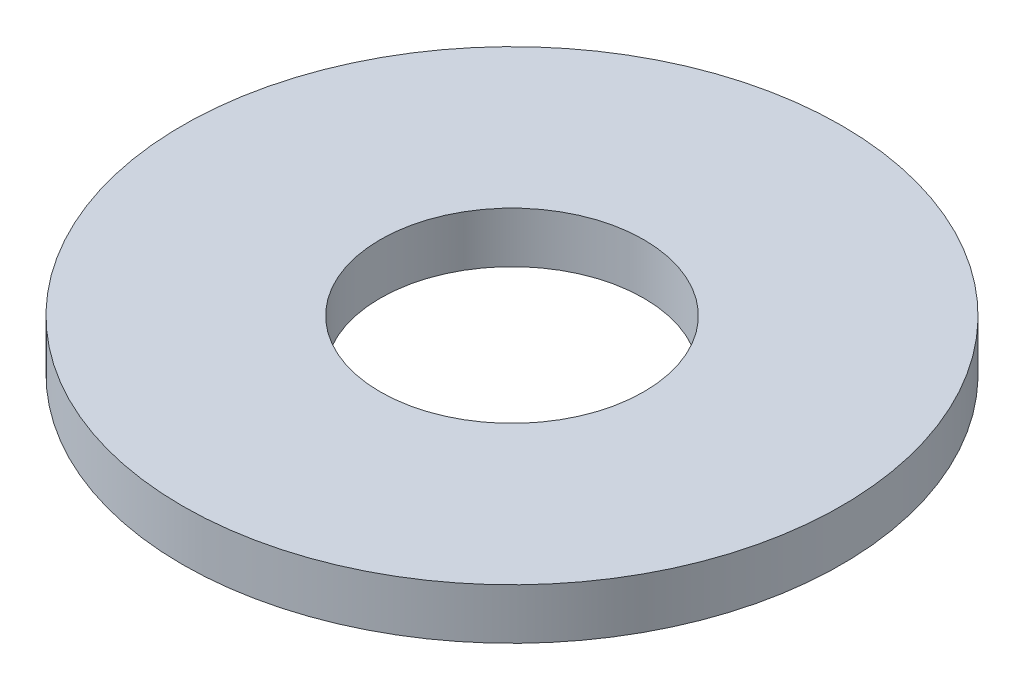
SolidWorks part; units mm, degrees
material "1060 Alloy"
ref_plane "Front Plane" through (0, 0, 0) normal (0, 0, 1) x (1, 0, 0)
ref_plane "Top Plane" through (0, 0, 0) normal (0, 1, 0) x (1, 0, 0)
ref_plane "Right Plane" through (0, 0, 0) normal (1, 0, 0) x (0, 0, -1)
sketch "Sketch1" plane through (0, 0, 0) normal (0, 1, 0) x (1, 0, 0)
  line L1 (2.7424, -4.75) -> (5.4848, 0)
  line L2 (5.4848, 0) -> (2.7424, 4.75)
  line L3 (2.7424, 4.75) -> (-2.7424, 4.75)
  line L4 (-2.7424, 4.75) -> (-5.4848, 0)
  line L5 (-5.4848, 0) -> (-2.7424, -4.75)
  line L6 (-2.7424, -4.75) -> (2.7424, -4.75)
  circle A0 centre (0, 0) radius 4.75 construction
  circle A2 centre (0, 0) radius 6.5
  circle A3 centre (0, 0) radius 2.6
  point P12 (0, 0)
  dimension "D2" = 5.2
  dimension "D1" = 9.5
  dimension "D3" = 13
extrude "Boss-Extrude1" add sketch "Sketch1" against normal blind 1 contours A2 L6 L5 L4 L3 L2 L1 | L5 L6 L1 L2 L3 L4 A3
scale "Scale1" scale about centroid uniform scaling yes scale factor 0.6
